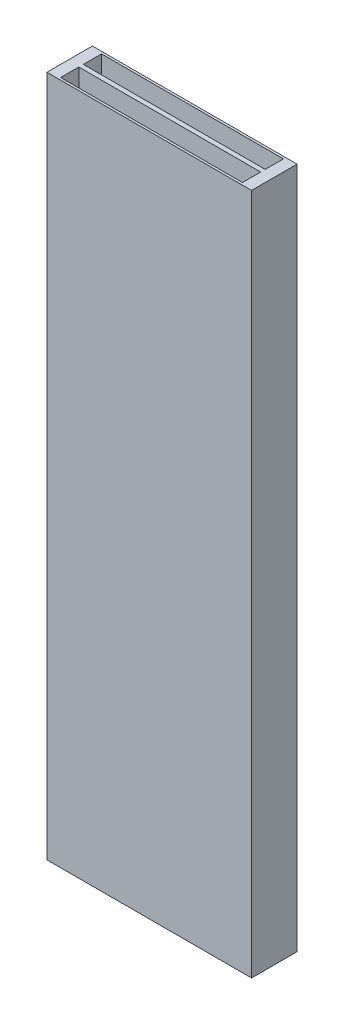
SolidWorks part; units mm, degrees
ref_plane "Front Plane" through (0, 0, 0) normal (0, 0, 1) x (1, 0, 0)
ref_plane "Top Plane" through (0, 0, 0) normal (0, 1, 0) x (1, 0, 0)
ref_plane "Right Plane" through (0, 0, 0) normal (1, 0, 0) x (0, 0, -1)
sketch "Sketch1" plane through (0, 0, 0) normal (0, 1, 0) x (1, 0, 0)
  line L1 (-4.5, -1) -> (4.5, -1)
  line L2 (-4.5, -1) -> (-4.5, 1)
  line L3 (-4.5, 1) -> (4.5, 1)
  line L4 (4.5, -1) -> (4.5, 1)
  line L5 (-4.5, -1) -> (4.5, 1) construction
  line L6 (-4.5, 1) -> (4.5, -1) construction
  point P0 (0, 0)
  dimension "D1" = 9
  dimension "D2" = 2
extrude "Boss-Extrude1" add sketch "Sketch1" along normal mid plane 30
sketch "Sketch2" plane through (0, 15, 0) normal (0, 1, 0) x (1, 0, 0)
  line L1 (-4, 0.1) -> (4, 0.1)
  line L2 (-4, 0.1) -> (-4, 0.9)
  line L3 (-4, 0.9) -> (4, 0.9)
  line L4 (4, 0.1) -> (4, 0.9)
  line L5 (-4, 0.1) -> (4, 0.9) construction
  line L6 (-4, 0.9) -> (4, 0.1) construction
  point P0 (0, 0.5)
  dimension "D1" = 0.8
  dimension "D2" = 8
  dimension "D3" = 0
  dimension "D4" = 0.5
extrude "Cut-Extrude1" cut sketch "Sketch2" against normal through all and the other way through all
mirror "Mirror1" about plane through (0, 0, 0) normal (0, 0, 1) of "Cut-Extrude1"
